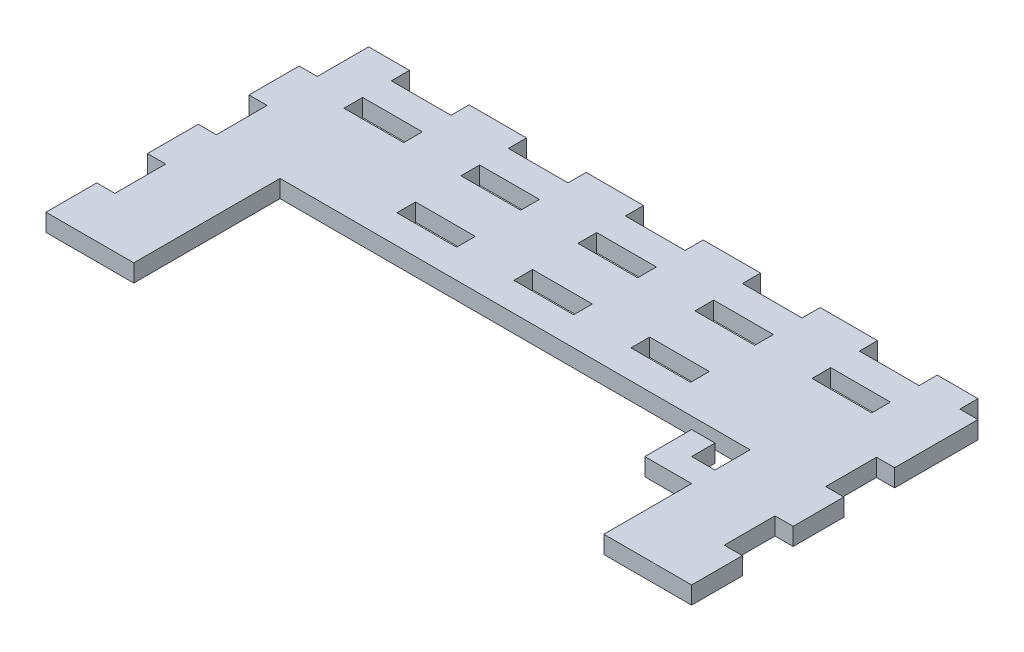
SolidWorks part; units mm, degrees
ref_plane "Front Plane" through (0, 0, 0) normal (0, 0, 1) x (1, 0, 0)
ref_plane "Top Plane" through (0, 0, 0) normal (0, 1, 0) x (1, 0, 0)
ref_plane "Right Plane" through (0, 0, 0) normal (1, 0, 0) x (0, 0, -1)
sketch "Sketch1" plane through (0, 0, 0) normal (0, 1, 0) x (1, 0, 0)
  line L0 (15, 0) -> (15, 25)
  line L1 (0, 0) -> (110.3444, 0) construction
  line L2 (0, 0) -> (0, 52.05)
  line L3 (0, 52.05) -> (110.3444, 52.05)
  line L4 (110.3444, 0) -> (110.3444, 52.05)
  line L5 (15, 25) -> (95.3444, 25)
  line L6 (95.3444, 25) -> (95.3444, 0)
  line L7 (55.1722, 0) -> (55.1722, 25) construction
  line L8 (15, 0) -> (0, 0)
  line L9 (95.3444, 0) -> (110.3444, 0)
  line L10 (0, 25) -> (110.3444, 25) construction
  dimension "D1" = 15
extrude "Boss-Extrude1" add sketch "Sketch1" against normal up to vertex (3 mm away)
sketch "Sketch2" plane through (0, 0, 0) normal (0, 1, 0) x (1, 0, 0)
  line L0 (3, 52.05) -> (3, 0) construction
  line L1 (15, 0) -> (0, 0) construction
  line L2 (0, 52.05) -> (110.3444, 52.05) construction
  line L3 (107.3444, 0) -> (107.3444, 52.05) construction
  line L4 (95.3444, 0) -> (110.3444, 0) construction
  line L5 (0, 0) -> (0, 52.05) construction
  line L6 (15, 0) -> (15, 25) construction
  line L7 (110.3444, 0) -> (110.3444, 52.05) construction
  line L8 (95.3444, 25) -> (95.3444, 0) construction
  line L9 (15, 25) -> (15, 30) construction
  line L10 (0, 0) -> (0, 52.05) construction
  line L11 (0, 52.05) -> (110.3444, 52.05) construction
  line L12 (15, 0) -> (0, 0) construction
  line L13 (15, 0) -> (15, 25) construction
  line L14 (110.3444, 0) -> (110.3444, 52.05) construction
  line L15 (95.3444, 0) -> (110.3444, 0) construction
  line L16 (95.3444, 25) -> (95.3444, 0) construction
  line L17 (0, 25) -> (110.3444, 25) construction
  line L18 (3, 43.375) -> (0, 43.375) construction
  line L19 (3, 34.6) -> (0, 34.6) construction
  line L20 (3, 26.125) -> (0, 26.125) construction
  line L21 (3, 17.25) -> (0, 17.25) construction
  line L22 (3, 8.775) -> (0, 8.775) construction
  line L23 (55.1722, 0) -> (55.1722, 52.05) construction
  line L24 (0, 33) -> (110.3444, 33) construction
  line L25 (15, 25) -> (95.3444, 25) construction
  line L26 (50.1722, 49.05) -> (60.1722, 49.05) construction
  line L27 (50.1722, 49.05) -> (40.1722, 49.05) construction
  line L28 (40.1722, 49.05) -> (30.1722, 49.05) construction
  line L29 (30.1722, 49.05) -> (20.1722, 49.05) construction
  line L30 (20.1722, 49.05) -> (10.1722, 49.05) construction
  line L31 (10.1722, 49.05) -> (10.1722, 52.05) construction
  line L32 (20.1722, 49.05) -> (20.1722, 52.05) construction
  line L33 (30.1722, 49.05) -> (30.1722, 52.05) construction
  line L34 (40.1722, 49.05) -> (40.1722, 52.05) construction
  line L35 (50.1722, 49.05) -> (50.1722, 52.05) construction
  line L36 (50.1722, 33) -> (50.1722, 30) construction
  line L37 (60.1722, 33) -> (60.1722, 30) construction
  line L38 (40.1722, 33) -> (40.1722, 30) construction
  line L39 (30.1722, 33) -> (30.1722, 30) construction
  line L40 (50.1722, 43.95) -> (60.1722, 43.95) construction
  line L41 (60.1722, 43.95) -> (60.1722, 40.95) construction
  line L42 (60.1722, 40.95) -> (50.1722, 40.95) construction
  line L43 (50.1722, 40.95) -> (50.1722, 43.95) construction
  line L44 (60.1722, 49.05) -> (60.1722, 52.05) construction
  line L45 (50.1722, 40.95) -> (40.1722, 40.95) construction
  line L46 (0, 40.95) -> (110.3444, 40.95) construction
  line L47 (40.1722, 40.95) -> (30.1722, 40.95) construction
  line L48 (30.1722, 40.95) -> (20.1722, 40.95) construction
  line L49 (20.1722, 40.95) -> (10.1722, 40.95) construction
  line L50 (10.1722, 40.95) -> (10.1722, 43.95) construction
  line L51 (0, 43.95) -> (110.3444, 43.95) construction
  line L52 (10.1722, 43.95) -> (20.1722, 43.95) construction
  line L53 (20.1722, 43.95) -> (20.1722, 40.95) construction
  line L54 (20.1722, 43.95) -> (30.1722, 43.95) construction
  line L55 (30.1722, 43.95) -> (30.1722, 40.95) construction
  line L56 (30.1722, 43.95) -> (40.1722, 43.95) construction
  line L57 (40.1722, 43.95) -> (40.1722, 40.95) construction
  line L58 (40.1722, 43.95) -> (50.1722, 43.95) construction
  line L59 (15, 30) -> (95.3444, 30) construction
  line L60 (95.3444, 30) -> (95.3444, 25) construction
  line L61 (110.3444, 30) -> (0, 30) construction
  dimension "D1" = 10
sketch "Sketch3" plane through (0, 0, 0) normal (0, 1, 0) x (1, 0, 0)
  line L0 (1.5, 52.15) -> (1.5, 52.05) construction
  line L1 (-0.1, 52.15) -> (3.1, 52.15)
  line L2 (-0.1, 52.15) -> (-0.1, 43.275)
  line L3 (-0.1, 43.275) -> (3.1, 43.275)
  line L4 (3.1, 52.15) -> (3.1, 43.275)
  line L5 (-0.1, 34.7) -> (3.1, 34.7)
  line L6 (-0.1, 34.7) -> (-0.1, 26.025)
  line L7 (-0.1, 26.025) -> (3.1, 26.025)
  line L8 (3.1, 34.7) -> (3.1, 26.025)
  line L9 (-0.1, 17.35) -> (3.1, 17.35)
  line L10 (-0.1, 17.35) -> (-0.1, 8.675)
  line L11 (-0.1, 8.675) -> (3.1, 8.675)
  line L12 (3.1, 17.35) -> (3.1, 8.675)
  line L13 (3.1, 47.7125) -> (3, 47.7125) construction
  line L14 (-0.1, 47.7125) -> (0, 47.7125) construction
  line L15 (1.5, 43.275) -> (1.5, 43.375) construction
  line L16 (3, 52.05) -> (3, 0) construction
  line L17 (0, 0) -> (0, 52.05) construction
  line L18 (0, 52.05) -> (110.3444, 52.05) construction
  line L19 (3, 43.375) -> (0, 43.375) construction
  line L20 (0, 52.15) -> (0, 52.05) construction
  line L21 (1.5, 34.7) -> (1.5, 34.6) construction
  line L22 (1.5, 26.025) -> (1.5, 26.125) construction
  line L23 (1.5, 8.675) -> (1.5, 8.775) construction
  line L24 (1.5, 17.35) -> (1.5, 17.25) construction
  line L25 (3, 8.775) -> (0, 8.775) construction
  line L26 (3, 17.25) -> (0, 17.25) construction
  line L27 (3, 34.6) -> (0, 34.6) construction
  line L28 (3, 26.125) -> (0, 26.125) construction
  line L29 (107.2444, 52.15) -> (107.2444, 48.95)
  line L30 (50.0722, 52.15) -> (60.2722, 52.15)
  line L31 (50.0722, 52.15) -> (50.0722, 48.95)
  line L32 (50.0722, 48.95) -> (60.2722, 48.95)
  line L33 (60.2722, 52.15) -> (60.2722, 48.95)
  line L34 (50.0722, 44.05) -> (60.2722, 44.05)
  line L35 (50.0722, 44.05) -> (50.0722, 40.85)
  line L36 (50.0722, 40.85) -> (60.2722, 40.85)
  line L37 (60.2722, 44.05) -> (60.2722, 40.85)
  line L38 (50.0722, 33.1) -> (60.2722, 33.1)
  line L39 (50.0722, 33.1) -> (50.0722, 29.9)
  line L40 (50.0722, 29.9) -> (60.2722, 29.9)
  line L41 (60.2722, 33.1) -> (60.2722, 29.9)
  line L42 (30.0722, 52.15) -> (40.2722, 52.15)
  line L43 (30.0722, 52.15) -> (30.0722, 48.95)
  line L44 (30.0722, 48.95) -> (40.2722, 48.95)
  line L45 (40.2722, 52.15) -> (40.2722, 48.95)
  line L46 (30.0722, 44.05) -> (40.2722, 44.05)
  line L47 (30.0722, 44.05) -> (30.0722, 40.85)
  line L48 (30.0722, 40.85) -> (40.2722, 40.85)
  line L49 (40.2722, 44.05) -> (40.2722, 40.85)
  line L50 (30.0722, 33.1) -> (40.2722, 33.1)
  line L51 (30.0722, 33.1) -> (30.0722, 29.9)
  line L52 (30.0722, 29.9) -> (40.2722, 29.9)
  line L53 (40.2722, 33.1) -> (40.2722, 29.9)
  line L54 (10.0722, 52.15) -> (20.2722, 52.15)
  line L55 (10.0722, 52.15) -> (10.0722, 48.95)
  line L56 (10.0722, 48.95) -> (20.2722, 48.95)
  line L57 (20.2722, 52.15) -> (20.2722, 48.95)
  line L58 (10.0722, 44.05) -> (20.2722, 44.05)
  line L59 (10.0722, 44.05) -> (10.0722, 40.85)
  line L60 (10.0722, 40.85) -> (20.2722, 40.85)
  line L61 (20.2722, 44.05) -> (20.2722, 40.85)
  line L62 (50.0722, 50.55) -> (50.1722, 50.55) construction
  line L63 (55.1722, 48.95) -> (55.1722, 49.05) construction
  line L64 (50.1722, 49.05) -> (60.1722, 49.05) construction
  line L65 (50.1722, 49.05) -> (50.1722, 52.05) construction
  line L66 (60.2722, 50.55) -> (60.1722, 50.55) construction
  line L67 (60.1722, 49.05) -> (60.1722, 52.05) construction
  line L68 (55.1722, 52.15) -> (55.1722, 52.05) construction
  line L69 (30.0722, 50.55) -> (30.1722, 50.55) construction
  line L70 (40.2722, 50.55) -> (40.1722, 50.55) construction
  line L71 (35.1722, 52.15) -> (35.1722, 52.05) construction
  line L72 (40.1722, 49.05) -> (40.1722, 52.05) construction
  line L73 (30.1722, 49.05) -> (30.1722, 52.05) construction
  line L74 (40.2722, 42.45) -> (40.1722, 42.45) construction
  line L75 (30.0722, 42.45) -> (30.1722, 42.45) construction
  line L76 (35.1722, 44.05) -> (35.1722, 43.95) construction
  line L77 (30.1722, 43.95) -> (40.1722, 43.95) construction
  line L78 (40.1722, 43.95) -> (40.1722, 40.95) construction
  line L79 (30.1722, 43.95) -> (30.1722, 40.95) construction
  line L80 (35.1722, 40.85) -> (35.1722, 40.95) construction
  line L81 (40.1722, 40.95) -> (30.1722, 40.95) construction
  line L82 (110.4444, 52.15) -> (110.4444, 48.95)
  line L83 (35.1722, 33.1) -> (35.1722, 33) construction
  line L84 (35.1722, 29.9) -> (35.1722, 30) construction
  line L85 (40.2722, 31.5) -> (40.1722, 31.5) construction
  line L86 (40.1722, 33) -> (40.1722, 30) construction
  line L87 (0, 33) -> (110.3444, 33) construction
  line L89 (10.0722, 50.55) -> (10.1722, 50.55) construction
  line L90 (20.2722, 50.55) -> (20.1722, 50.55) construction
  line L91 (10.1722, 49.05) -> (10.1722, 52.05) construction
  line L92 (20.1722, 49.05) -> (20.1722, 52.05) construction
  line L93 (15, 30) -> (95.3444, 30) construction
  line L94 (55.1722, 0) -> (55.1722, 52.05) construction
  line L95 (110.4444, 17.35) -> (107.2444, 17.35)
  line L96 (110.4444, 17.35) -> (110.4444, 8.675)
  line L97 (110.4444, 8.675) -> (107.2444, 8.675)
  line L98 (107.2444, 17.35) -> (107.2444, 8.675)
  line L99 (110.4444, 34.7) -> (107.2444, 34.7)
  line L100 (110.4444, 34.7) -> (110.4444, 26.025)
  line L101 (110.4444, 26.025) -> (107.2444, 26.025)
  line L102 (107.2444, 34.7) -> (107.2444, 26.025)
  line L103 (110.4444, 52.15) -> (107.2444, 52.15)
  line L104 (110.4444, 52.15) -> (110.4444, 43.275) construction
  line L105 (110.4444, 43.275) -> (107.2444, 43.275) construction
  line L106 (107.2444, 52.15) -> (107.2444, 43.275) construction
  line L107 (100.2722, 52.15) -> (100.2722, 48.95)
  line L108 (100.2722, 52.15) -> (90.0722, 52.15)
  line L109 (90.0722, 52.15) -> (90.0722, 48.95)
  line L110 (100.2722, 48.95) -> (90.0722, 48.95)
  line L111 (100.2722, 44.05) -> (100.2722, 40.85)
  line L112 (100.2722, 40.85) -> (90.0722, 40.85)
  line L113 (90.0722, 44.05) -> (90.0722, 40.85)
  line L114 (100.2722, 44.05) -> (90.0722, 44.05)
  line L115 (80.2722, 33.1) -> (80.2722, 29.9)
  line L116 (80.2722, 29.9) -> (70.0722, 29.9)
  line L117 (70.0722, 33.1) -> (70.0722, 29.9)
  line L118 (80.2722, 33.1) -> (70.0722, 33.1)
  line L119 (80.2722, 44.05) -> (80.2722, 40.85)
  line L120 (80.2722, 44.05) -> (70.0722, 44.05)
  line L121 (70.0722, 44.05) -> (70.0722, 40.85)
  line L122 (80.2722, 40.85) -> (70.0722, 40.85)
  line L123 (80.2722, 52.15) -> (80.2722, 48.95)
  line L124 (80.2722, 52.15) -> (70.0722, 52.15)
  line L125 (70.0722, 52.15) -> (70.0722, 48.95)
  line L126 (80.2722, 48.95) -> (70.0722, 48.95)
  line L127 (107.2444, 48.95) -> (110.4444, 48.95)
extrude "Cut-Extrude1" cut sketch "Sketch3" against normal through all
sketch "Sketch4" plane through (0, 0, 0) normal (0, 1, 0) x (1, 0, 0)
  line L0 (91.3444, 15) -> (91.3444, 19) construction
  line L1 (95.3444, 25) -> (87.3444, 25) construction
  line L2 (95.3444, 25) -> (95.3444, 15) construction
  line L3 (95.3444, 15) -> (87.3444, 15)
  line L4 (87.3444, 25) -> (87.3444, 15) construction
  line L5 (91.3444, 19) -> (91.3444, 23)
  line L6 (91.3444, 23) -> (95.3444, 23) construction
  line L7 (87.3444, 15) -> (87.3444, 23)
  line L8 (87.3444, 23) -> (91.3444, 23)
  line L9 (91.3444, 19) -> (95.3444, 19)
  line L10 (95.3444, 19) -> (95.3444, 15)
  dimension "D2" = 2
  dimension "D1" = 4
extrude "Boss-Extrude2" add sketch "Sketch4" against normal up to surface (3 mm away) up to face at (55.1722, -3, -35.324)
